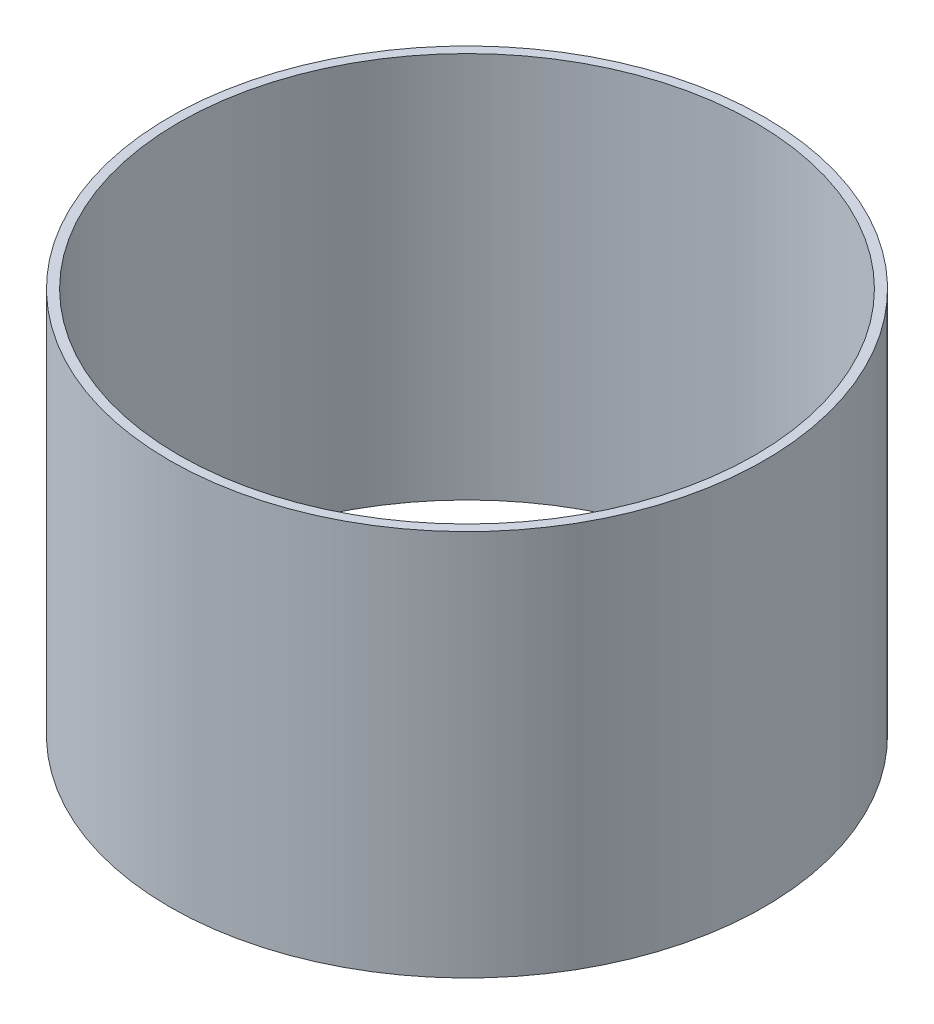
SolidWorks part; units mm, degrees
material "6061-T6 (SS)"
ref_plane "Front Plane" through (0, 0, 0) normal (0, 0, 1) x (1, 0, 0)
ref_plane "Top Plane" through (0, 0, 0) normal (0, 1, 0) x (1, 0, 0)
ref_plane "Right Plane" through (0, 0, 0) normal (1, 0, 0) x (0, 0, -1)
sketch "Sketch1" plane through (0, 0, 0) normal (0, 1, 0) x (1, 0, 0)
  circle A0 centre (0, 0) radius 152.4
  circle A1 centre (0, 0) radius 147.6375
  dimension "D1" = 304.8
  dimension "D2" = 4.7625
extrude "Boss-Extrude1" add sketch "Sketch1" along normal blind 198.12
ref_plane "Plane1" through (-152.4, 0, 0) normal (-1, 0, 0) x (0, 0, 1)
ref_plane "Plane2" through (0, 99.06, 0) normal (0, 1, 0) x (1, 0, 0)
